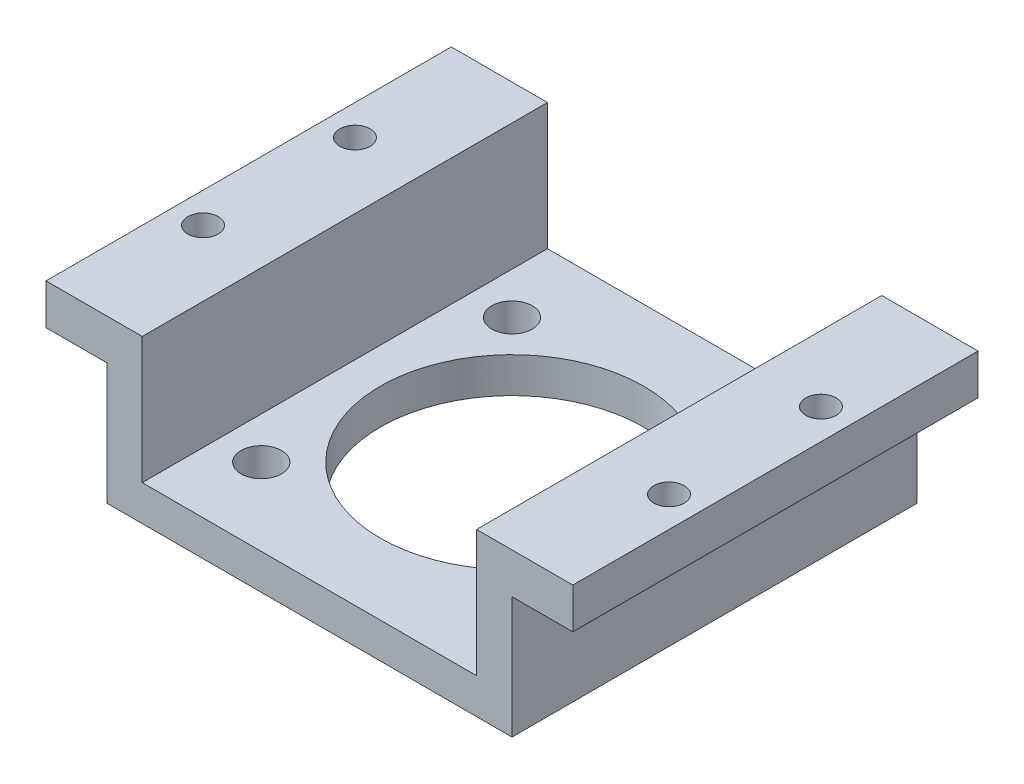
SolidWorks part; units mm, degrees
material "6061 合金"
ref_plane "前视基准面" through (0, 0, 0) normal (0, 0, 1) x (1, 0, 0)
ref_plane "上视基准面" through (0, 0, 0) normal (0, 1, 0) x (1, 0, 0)
ref_plane "右视基准面" through (0, 0, 0) normal (1, 0, 0) x (0, 0, -1)
sketch "草图1" plane through (0, 0, 0) normal (0, 0, 1) x (1, 0, 0)
  line L0 (0, 0) -> (0, 41.1065) construction
  line L1 (-16.5, 27.3988) -> (-16.5, 16.3988)
  line L2 (-26, 27.3988) -> (-16.5, 27.3988)
  line L3 (-26, 27.3988) -> (-26, 21.3988)
  line L4 (-20, 11.3988) -> (20, 11.3988)
  line L5 (26, 27.3988) -> (26, 21.3988)
  line L6 (-26, 21.3988) -> (-20, 21.3988)
  line L7 (16.5, 27.3988) -> (26, 27.3988)
  line L9 (-20, 21.3988) -> (-20, 11.3988)
  line L10 (20, 16.3988) -> (20, 11.3988)
  line L11 (20, 16.3988) -> (20, 21.3988)
  line L12 (20, 21.3988) -> (26, 21.3988)
  line L13 (-16.5, 16.3988) -> (16.5, 16.3988)
  line L14 (16.5, 16.3988) -> (16.5, 27.3988)
  dimension "D1" = 52
  dimension "D2" = 6
  dimension "D3" = 6
  dimension "D4" = 5
  dimension "D5" = 3.5
  dimension "D6" = 9.5
  dimension "D7" = 11
extrude "凸台-拉伸1" add sketch "草图1" along normal blind 40
sketch "草图2" plane through (0, 11.3988, 0) normal (0, -1, 0) x (1, 0, 0)
  line L1 (-20, 20) -> (20, 20) construction
  line L2 (-20, 40) -> (-20, 0) construction
  line L3 (20, 40) -> (20, 0) construction
  circle A0 centre (0, 20) radius 13
  dimension "D1" = 26
extrude "切除-拉伸1" cut sketch "草图2" against normal blind 1.5
sketch "草图3" plane through (0, 12.8988, 0) normal (0, -1, 0) x (1, 0, 0)
  circle A0 centre (0, 20) radius 13
  dimension "D1" = 26
extrude "切除-拉伸2" cut sketch "草图3" against normal through all
sketch "草图4" plane through (0, 11.3988, 0) normal (0, -1, 0) x (1, 0, 0)
  line L0 (0, 20) -> (0, 33.6149) construction
  line L1 (0, 20) -> (13.7279, 33.7279) construction
  circle A0 centre (12.3744, 32.3744) radius 2
  dimension "D2" = 4
  dimension "D3" = 17.5
  dimension "D1" = 45
extrude "切除-拉伸3" cut sketch "草图4" against normal up to next (5 mm away)
pattern_circular "阵列(圆周)1" count 4 over 360 about axis through (0, 0, 20) along (0, 1, 0) of "切除-拉伸3"
sketch "草图5" plane through (0, 21.3988, 0) normal (0, -1, 0) x (1, 0, 0)
  line L0 (-26, 20) -> (-20, 20) construction
  line L1 (-26, 40) -> (-26, 0) construction
  line L2 (-20, 40) -> (-20, 0) construction
  line L3 (-23, 40) -> (-23, 0) construction
  line L4 (-26, 40) -> (-20, 40) construction
  line L5 (-26, 0) -> (-20, 0) construction
  circle A0 centre (-23, 27.5) radius 1.5
  circle A1 centre (-23, 12.5) radius 1.5
  dimension "D1" = 3
  dimension "D3" = 15
  dimension "D4" = 7.5
extrude "切除-拉伸4" cut sketch "草图5" against normal through all
ref_plane "基准面1" through (0, 0, 0) normal (-1, 0, 0) x (0, 0, 1)
mirror "镜向1" about plane through (0, 0, 0) normal (-1, 0, 0) of "切除-拉伸4"
sketch "草图6" plane through (0, 16.3988, 0) normal (0, 1, 0) x (1, 0, 0)
  line L4 (16.5, 0) -> (-16.5, 0)
  line L5 (-16.5, 0) -> (-16.5, -40)
  line L6 (-16.5, -40) -> (16.5, -40)
  line L7 (16.5, -40) -> (16.5, 0)
  line L8 (16.5, 0) -> (-16.5, 0)
  line L9 (-16.5, 0) -> (-16.5, -40)
  line L10 (-16.5, -40) -> (16.5, -40)
  line L11 (16.5, -40) -> (16.5, 0)
  dimension "D1" = 0
extrude "切除-拉伸5" cut sketch "草图6" against normal blind 1.5
sketch "草图7" plane through (0, 21.3988, 0) normal (0, -1, 0) x (1, 0, 0)
  line L0 (-26, 0) -> (-20, 0) construction
  line L1 (-20, 0) -> (-20, 40) construction
  line L2 (-20, 40) -> (-26, 40) construction
  line L3 (-26, 40) -> (-26, 0) construction
  line L4 (20, 0) -> (26, 0) construction
  line L5 (26, 0) -> (26, 40) construction
  line L6 (26, 40) -> (20, 40) construction
  line L7 (20, 40) -> (20, 0) construction
  line L8 (-26, 0) -> (-20, 0)
  line L9 (-20, 0) -> (-20, 40)
  line L10 (-20, 40) -> (-26, 40)
  line L11 (-26, 40) -> (-26, 0)
  line L12 (20, 0) -> (26, 0)
  line L13 (26, 0) -> (26, 40)
  line L14 (26, 40) -> (20, 40)
  line L15 (20, 40) -> (20, 0)
extrude "切除-拉伸6" cut sketch "草图7" against normal blind 2
